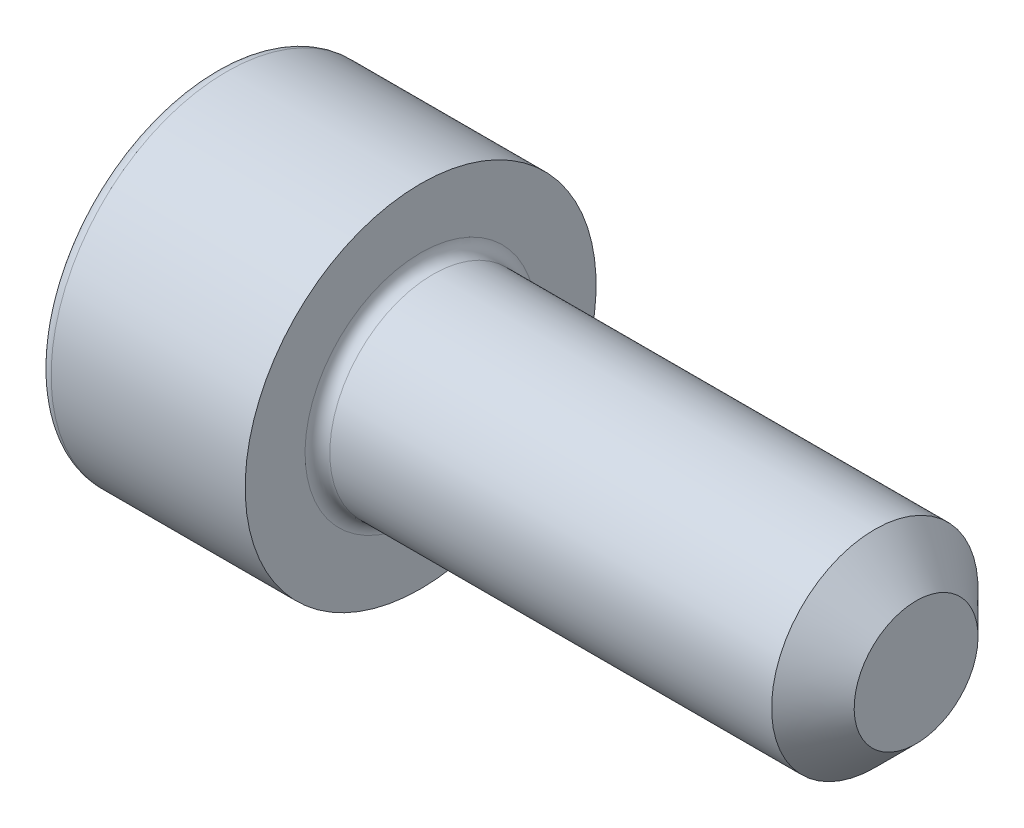
SolidWorks part; units mm, degrees
ref_plane "Спереди" through (0, 0, 0) normal (0, 0, 1) x (1, 0, 0)
ref_plane "Сверху" through (0, 0, 0) normal (0, 1, 0) x (1, 0, 0)
ref_plane "Справа" through (0, 0, 0) normal (1, 0, 0) x (0, 0, -1)
sketch "Эскиз1" plane through (0, 0, 0) normal (0, 0, 1) x (1, 0, 0)
  line L0 (0, 0) -> (0, 4.25)
  line L1 (0, 4.25) -> (5, 4.25)
  line L2 (5, 4.25) -> (5, 2.5)
  line L3 (5, 2.5) -> (17, 2.5)
  line L4 (17, 2.5) -> (17, 0)
  line L5 (17, 0) -> (0, 0) construction
  line L6 (0, 0) -> (17, 0)
  dimension "D1" = 8.5
  dimension "D2" = 5
  dimension "D3" = 5
  dimension "D4" = 12
revolve "Повернуть1" add sketch "Эскиз1" angle 360 about L5
cosmetic thread "Условное изображение резьбы1" parameters "D2"=4.11
sketch "Эскиз2" plane through (0, 0, 0) normal (-1, 0, 0) x (0, 0, 1)
  line L1 (-1.1547, 2) -> (-2.3094, 0)
  line L2 (-2.3094, 0) -> (-1.1547, -2)
  line L3 (-1.1547, -2) -> (1.1547, -2)
  line L4 (1.1547, -2) -> (2.3094, 0)
  line L5 (2.3094, 0) -> (1.1547, 2)
  line L6 (1.1547, 2) -> (-1.1547, 2)
  circle A0 centre (0, 0) radius 2 construction
  dimension "D1" = 4
extrude "Вырез-Вытянуть1" cut sketch "Эскиз2" against normal blind 2.5
fillet "Скругление1" radius 0.3 2 edges at (0, 4.25, 0) (5, 2.5, 0)
chamfer "Фаска1" distance 1 angle 45 1 edges at (17, 2.5, 0)
